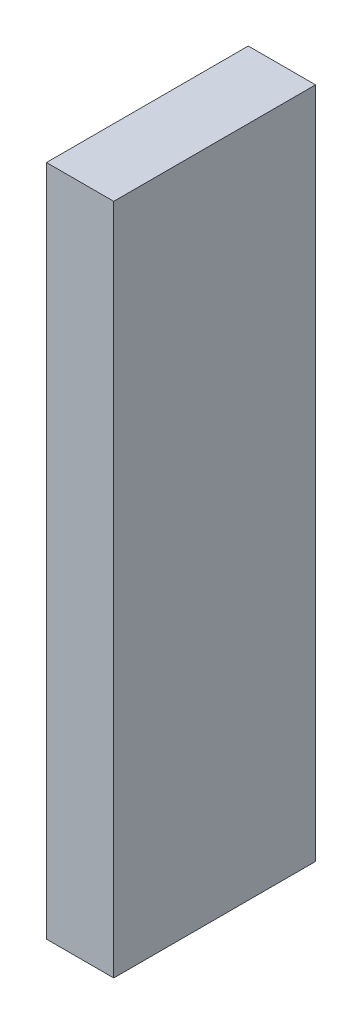
SolidWorks part; units mm, degrees
material "POLYURETHANE (11671)"
ref_plane "Front Plane" through (0, 0, 0) normal (0, 0, 1) x (1, 0, 0)
ref_plane "Top Plane" through (0, 0, 0) normal (0, 1, 0) x (1, 0, 0)
ref_plane "Right Plane" through (0, 0, 0) normal (1, 0, 0) x (0, 0, -1)
sketch "Sketch1" plane through (0, 0, 0) normal (1, 0, 0) x (0, 0, -1)
  line L1 (-4.7625, -15.875) -> (4.7625, -15.875)
  line L2 (-4.7625, -15.875) -> (-4.7625, 15.875)
  line L3 (-4.7625, 15.875) -> (4.7625, 15.875)
  line L4 (4.7625, -15.875) -> (4.7625, 15.875)
  line L5 (-4.7625, -15.875) -> (4.7625, 15.875) construction
  line L6 (-4.7625, 15.875) -> (4.7625, -15.875) construction
  point P0 (0, 0)
  dimension "D1" = 9.525
  dimension "D2" = 31.75
extrude "Boss-Extrude1" add sketch "Sketch1" along normal blind 3.175
